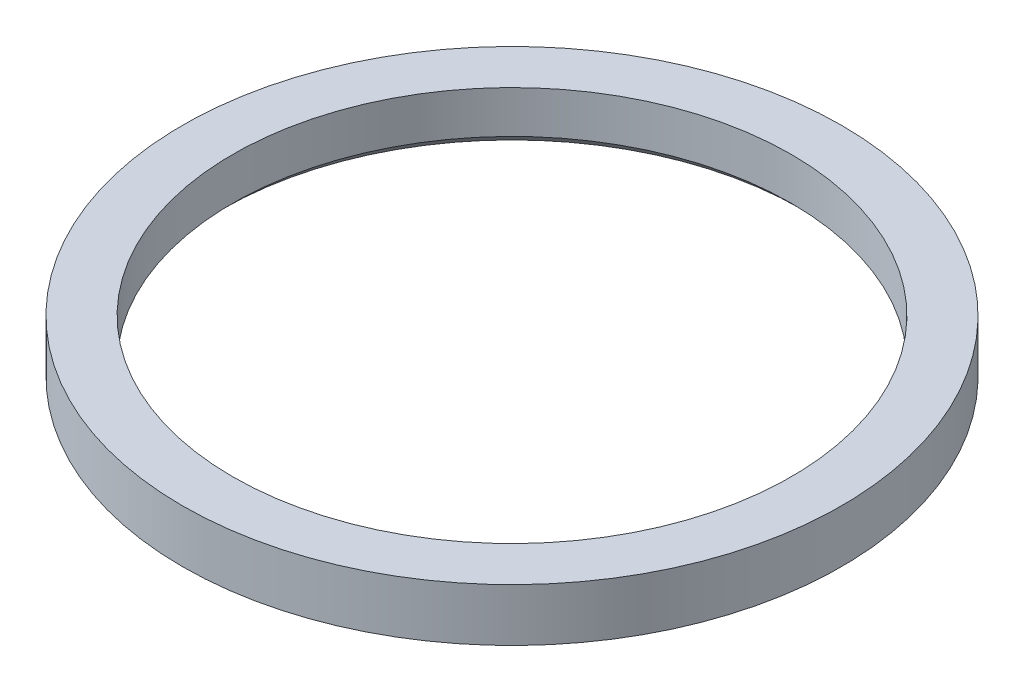
SolidWorks part; units mm, degrees
ref_plane "Front Plane" through (0, 0, 0) normal (0, 0, 1) x (1, 0, 0)
ref_plane "Top Plane" through (0, 0, 0) normal (0, 1, 0) x (1, 0, 0)
ref_plane "Right Plane" through (0, 0, 0) normal (1, 0, 0) x (0, 0, -1)
sketch "Sketch1" plane through (0, 0, 0) normal (0, 1, 0) x (1, 0, 0)
  circle A0 centre (0, 0) radius 9.5
  dimension "D1" = 19
extrude "Boss-Extrude1" add sketch "Sketch1" along normal blind 1.52
sketch "Sketch2" plane through (0, 1.52, 0) normal (0, 1, 0) x (1, 0, 0)
  circle A0 centre (0, 0) radius 8.05
  dimension "D1" = 16.1
extrude "Cut-Extrude1" cut sketch "Sketch2" against normal through all
chamfer "Chamfer1" distance 0.3 angle 45 1 edges at (0, 0, 8.05)
